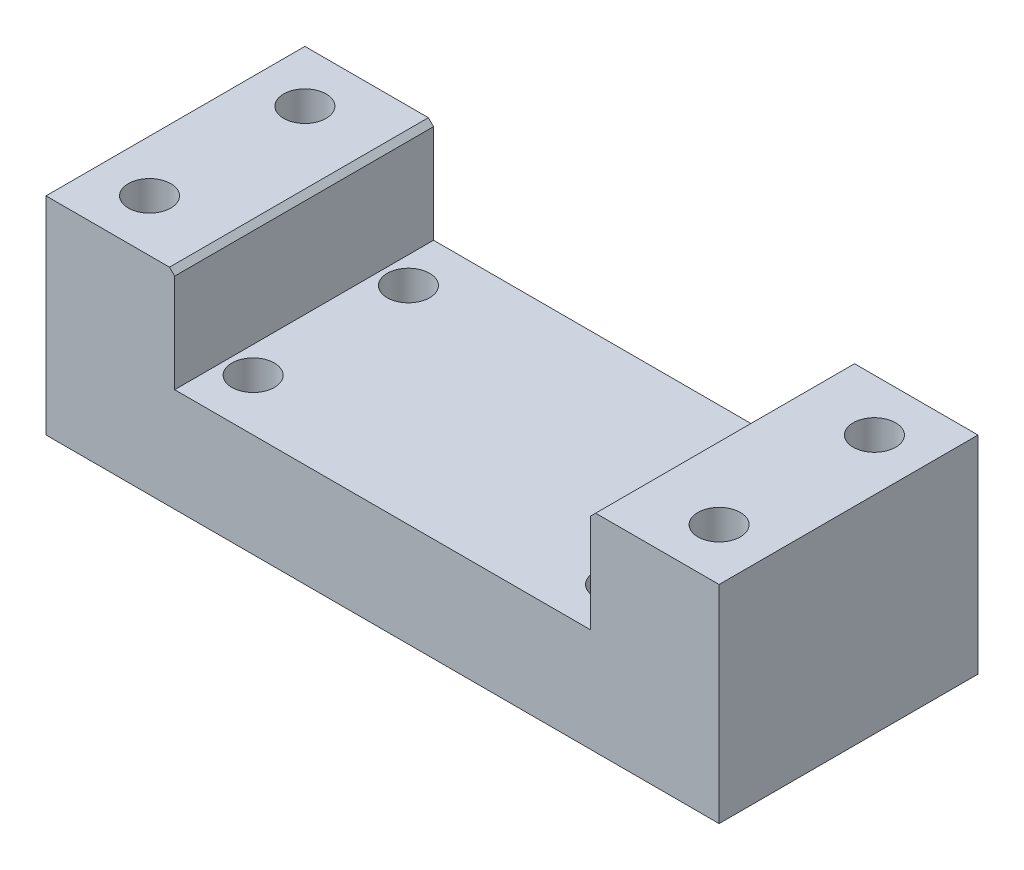
SolidWorks part; units mm, degrees
ref_plane "Спереди" through (0, 0, 0) normal (0, 0, 1) x (1, 0, 0)
ref_plane "Сверху" through (0, 0, 0) normal (0, 1, 0) x (1, 0, 0)
ref_plane "Справа" through (0, 0, 0) normal (1, 0, 0) x (0, 0, -1)
sketch "Sketch1" plane through (0, 0, 0) normal (0, 1, 0) x (1, 0, 0)
  line L1 (65, -25) -> (-65, -25)
  line L2 (65, -25) -> (65, 25)
  line L3 (65, 25) -> (-65, 25)
  line L4 (-65, -25) -> (-65, 25)
  line L5 (65, -25) -> (-65, 25) construction
  line L6 (65, 25) -> (-65, -25) construction
  point P0 (0, 0)
  dimension "D1" = 130
  dimension "D2" = 50
extrude "Boss-Extrude1" add sketch "Sketch1" along normal blind 40
sketch "Sketch2" plane through (0, 0, 25) normal (0, 0, 1) x (1, 0, 0)
  line L0 (-65, 40) -> (65, 40) construction
  line L1 (40.15, 60) -> (-40.15, 60)
  line L2 (40.15, 60) -> (40.15, 20)
  line L3 (40.15, 20) -> (-40.15, 20)
  line L4 (-40.15, 60) -> (-40.15, 20)
  line L5 (40.15, 60) -> (-40.15, 20) construction
  line L6 (40.15, 20) -> (-40.15, 60) construction
  point P0 (0, 40)
  dimension "D1" = 80.3
  dimension "D2" = 40
extrude "Cut-Extrude1" cut sketch "Sketch2" against normal through all
sketch "Sketch3" plane through (0, 0, 0) normal (0, -1, 0) x (1, 0, 0)
  line L1 (-35, -15) -> (35, -15) construction
  line L2 (-35, -15) -> (-35, 15) construction
  line L3 (-35, 15) -> (35, 15) construction
  line L4 (35, -15) -> (35, 15) construction
  line L5 (-35, -15) -> (35, 15) construction
  line L6 (-35, 15) -> (35, -15) construction
  circle A0 centre (-35, 15) radius 4.1
  circle A1 centre (-35, -15) radius 4.1
  circle A2 centre (35, -14.2173) radius 4.1
  circle A3 centre (35, 15) radius 4.1
  point P0 (0, 0)
  dimension "D3" = 8.2
  dimension "D1" = 30
  dimension "D2" = 70
extrude "Cut-Extrude2" cut sketch "Sketch3" against normal through all
chamfer "Chamfer1" distance 1 angle 45 2 edges at (40.15, 40, 0) (-40.15, 40, 0)
sketch "Sketch5" plane through (0, 0, 0) normal (0, -1, 0) x (1, 0, 0)
  line L1 (55, -15) -> (-55, -15) construction
  line L2 (55, -15) -> (55, 15) construction
  line L3 (55, 15) -> (-55, 15) construction
  line L4 (-55, -15) -> (-55, 15) construction
  line L5 (55, -15) -> (-55, 15) construction
  line L6 (55, 15) -> (-55, -15) construction
  circle A0 centre (-55, 15) radius 4.1
  circle A1 centre (-55, -15) radius 4.1
  circle A2 centre (55, 15) radius 4.1
  circle A3 centre (55, -15) radius 4.1
  point P0 (0, 0)
  dimension "D3" = 8.2
  dimension "D1" = 30
  dimension "D2" = 110
extrude "Cut-Extrude3" cut sketch "Sketch5" against normal through all
